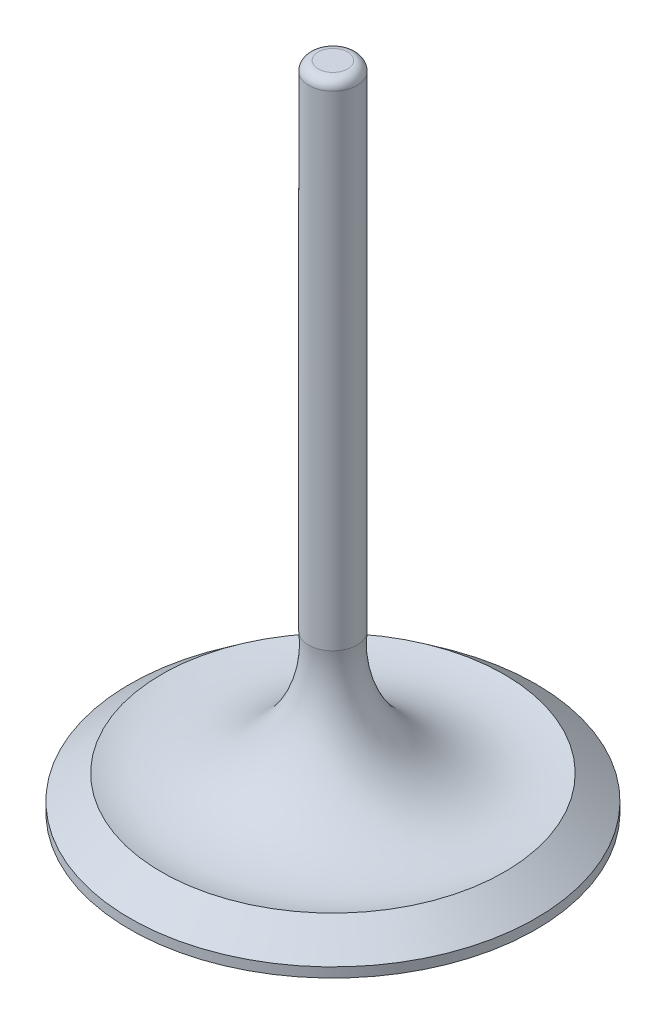
SolidWorks part; units mm, degrees
ref_plane "Front Plane" through (0, 0, 0) normal (0, 0, 1) x (1, 0, 0)
ref_plane "Top Plane" through (0, 0, 0) normal (0, 1, 0) x (1, 0, 0)
ref_plane "Right Plane" through (0, 0, 0) normal (1, 0, 0) x (0, 0, -1)
sketch "Sketch1" plane through (0, 0, 0) normal (1, 0, 0) x (0, 0, -1)
  line L0 (0, 0) -> (0, 85.55)
  line L1 (0, 85.55) -> (3.18, 85.55)
  line L2 (3.18, 85.55) -> (3.18, 20.6233)
  line L3 (0, 0) -> (26.67, 0)
  line L4 (26.67, 0) -> (26.67, 1.27)
  line L5 (26.67, 1.27) -> (22.5099, 4.45)
  arc A0 (3.18, 20.6233) -> (22.5099, 4.45) centre (18.3561, 19.1234) ccw
  point P7 (23.9583, 4.45)
  point P9 (18.3248, 19.6984)
  point P11 (22.3592, 4.45)
  point P12 (18.3561, 19.1234)
  dimension "D6" = 15.25
  dimension "D1" = 85.55
  dimension "D2" = 3.18
  dimension "D3" = 26.67
  dimension "D4" = 3.18
  dimension "D5" = 1.27
revolve "Revolve1" add sketch "Sketch1" angle 360 about L0
fillet "Fillet1" radius 1.25 1 edges at (0, 85.55, -3.18)
